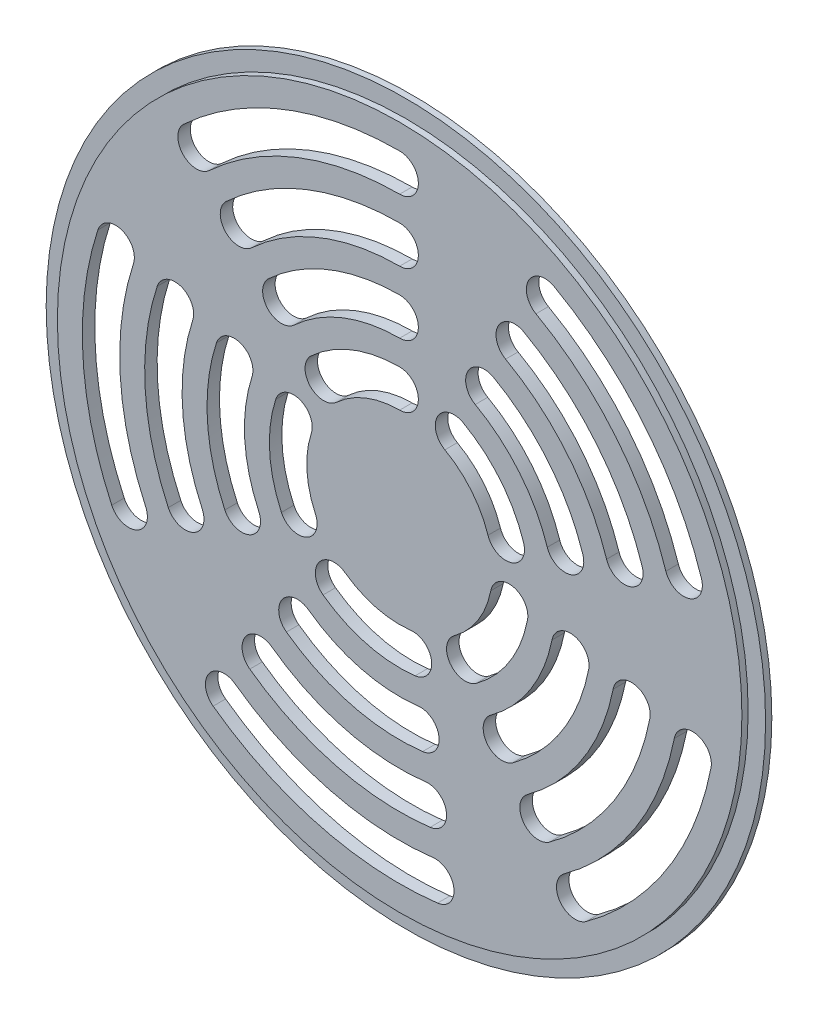
SolidWorks part; units mm, degrees
ref_plane "Plan de face" through (0, 0, 0) normal (0, 0, 1) x (1, 0, 0)
ref_plane "Plan de dessus" through (0, 0, 0) normal (0, 1, 0) x (1, 0, 0)
ref_plane "Plan de droite" through (0, 0, 0) normal (1, 0, 0) x (0, 0, -1)
sketch "Esquisse1" plane through (0, 0, 0) normal (0, 0, 1) x (1, 0, 0)
  line L0 (-32.5805, 35.1129) -> (-25.7788, 27.7825) construction
  line L1 (-25.7788, 27.7825) -> (0, 0) construction
  line L2 (23.3265, 41.8364) -> (18.4566, 33.1023) construction
  line L3 (46.9971, -9.2566) -> (37.1856, -7.3241) construction
  line L4 (5.7193, -47.5573) -> (4.5253, -37.6289) construction
  line L5 (-43.4623, -20.1354) -> (-34.3888, -15.9318) construction
  circle A0 centre (0, 0) radius 54.9
  arc A1 (0, 50.9) -> (-34.6211, 37.3121) centre (0, 0) ccw
  arc A2 (0, 44.9) -> (-30.54, 32.9138) centre (0, 0) ccw
  circle A3 centre (0, 47.9) radius 3
  circle A4 centre (-32.5805, 35.1129) radius 3
  arc A5 (48.4088, 15.729) -> (24.7874, 44.4567) centre (0, 0) ccw
  arc A6 (42.7024, 13.8749) -> (21.8655, 39.2162) centre (0, 0) ccw
  circle A7 centre (45.5556, 14.8019) radius 3
  circle A8 centre (23.3265, 41.8364) radius 3
  arc A9 (29.9183, -41.179) -> (49.9405, -9.8364) centre (0, 0) ccw
  arc A10 (26.3916, -36.3249) -> (44.0536, -8.6769) centre (0, 0) ccw
  circle A11 centre (28.1549, -38.7519) radius 3
  circle A12 centre (46.9971, -9.2566) radius 3
  arc A13 (-29.9183, -41.179) -> (6.0775, -50.5359) centre (0, 0) ccw
  arc A14 (-26.3916, -36.3249) -> (5.3611, -44.5788) centre (0, 0) ccw
  circle A15 centre (-28.1549, -38.7519) radius 3
  circle A16 centre (5.7193, -47.5573) radius 3
  arc A17 (-48.4088, 15.729) -> (-46.1844, -21.3965) centre (0, 0) ccw
  arc A18 (-42.7024, 13.8749) -> (-40.7403, -18.8743) centre (0, 0) ccw
  circle A19 centre (-45.5556, 14.8019) radius 3
  circle A20 centre (-43.4623, -20.1354) radius 3
  arc A21 (0, 40.9) -> (-27.8193, 29.9816) centre (0, 0) ccw
  arc A22 (0, 34.9) -> (-23.7382, 25.5833) centre (0, 0) ccw
  circle A23 centre (0, 37.9) radius 3
  circle A24 centre (-25.7788, 27.7825) radius 3
  arc A25 (38.8982, 12.6388) -> (19.9176, 35.7225) centre (0, 0) ccw
  arc A26 (33.1919, 10.7847) -> (16.9957, 30.4821) centre (0, 0) ccw
  circle A27 centre (36.045, 11.7117) radius 3
  circle A28 centre (18.4566, 33.1023) radius 3
  arc A29 (24.0404, -33.0888) -> (40.129, -7.9039) centre (0, 0) ccw
  arc A30 (20.5137, -28.2347) -> (34.2421, -6.7444) centre (0, 0) ccw
  circle A31 centre (22.2771, -30.6617) radius 3
  circle A32 centre (37.1856, -7.3241) radius 3
  arc A33 (-24.0404, -33.0888) -> (4.8835, -40.6074) centre (0, 0) ccw
  arc A34 (-20.5137, -28.2347) -> (4.1671, -34.6503) centre (0, 0) ccw
  circle A35 centre (-22.2771, -30.6617) radius 3
  circle A36 centre (4.5253, -37.6289) radius 3
  arc A37 (-38.8982, 12.6388) -> (-37.1108, -17.1929) centre (0, 0) ccw
  arc A38 (-33.1919, 10.7847) -> (-31.6667, -14.6707) centre (0, 0) ccw
  circle A39 centre (-36.045, 11.7117) radius 3
  circle A40 centre (-34.3888, -15.9318) radius 3
  arc A41 (0, 30.9) -> (-21.0175, 22.6511) centre (0, 0) ccw
  arc A42 (0, 24.9) -> (-16.9364, 18.2529) centre (0, 0) ccw
  circle A43 centre (0, 27.9) radius 3
  circle A44 centre (-18.977, 20.452) radius 3
  arc A45 (29.3876, 9.5486) -> (15.0478, 26.9884) centre (0, 0) ccw
  arc A46 (23.6813, 7.6945) -> (12.1259, 21.748) centre (0, 0) ccw
  circle A47 centre (26.5345, 8.6216) radius 3
  circle A48 centre (13.5868, 24.3682) radius 3
  arc A49 (18.1626, -24.9986) -> (30.3175, -5.9714) centre (0, 0) ccw
  arc A50 (14.6359, -20.1445) -> (24.4306, -4.8119) centre (0, 0) ccw
  circle A51 centre (16.3992, -22.5716) radius 3
  circle A52 centre (27.3741, -5.3916) radius 3
  arc A53 (-18.1626, -24.9986) -> (3.6895, -30.6789) centre (0, 0) ccw
  arc A54 (-14.6359, -20.1445) -> (2.9731, -24.7219) centre (0, 0) ccw
  circle A55 centre (-16.3992, -22.5716) radius 3
  circle A56 centre (3.3313, -27.7004) radius 3
  arc A57 (-29.3876, 9.5486) -> (-28.0373, -12.9892) centre (0, 0) ccw
  arc A58 (-23.6813, 7.6945) -> (-22.5932, -10.4671) centre (0, 0) ccw
  circle A59 centre (-26.5345, 8.6216) radius 3
  circle A60 centre (-25.3152, -11.7282) radius 3
  arc A61 (0, 20.9) -> (-14.2157, 15.3207) centre (0, 0) ccw
  arc A62 (0, 14.9) -> (-10.1347, 10.9224) centre (0, 0) ccw
  circle A63 centre (0, 17.9) radius 3
  circle A64 centre (-12.1752, 13.1215) radius 3
  arc A65 (19.8771, 6.4585) -> (10.1779, 18.2543) centre (0, 0) ccw
  arc A66 (14.1707, 4.6044) -> (7.256, 13.0138) centre (0, 0) ccw
  circle A67 centre (17.0239, 5.5314) radius 3
  circle A68 centre (8.717, 15.6341) radius 3
  arc A69 (12.2847, -16.9085) -> (20.506, -4.0389) centre (0, 0) ccw
  arc A70 (8.758, -12.0544) -> (14.6191, -2.8794) centre (0, 0) ccw
  circle A71 centre (10.5214, -14.4814) radius 3
  circle A72 centre (17.5626, -3.4592) radius 3
  arc A73 (-12.2847, -16.9085) -> (2.4955, -20.7505) centre (0, 0) ccw
  arc A74 (-8.758, -12.0544) -> (1.7791, -14.7934) centre (0, 0) ccw
  circle A75 centre (-10.5214, -14.4814) radius 3
  circle A76 centre (2.1373, -17.7719) radius 3
  arc A77 (-19.8771, 6.4585) -> (-18.9637, -8.7856) centre (0, 0) ccw
  arc A78 (-14.1707, 4.6044) -> (-13.5196, -6.2634) centre (0, 0) ccw
  circle A79 centre (-17.0239, 5.5314) radius 3
  circle A80 centre (-16.2417, -7.5245) radius 3
  point P46 (0, 0)
  point P92 (0, 0)
  point P134 (0, 0)
  point P144 (0, 0)
  point P145 (0, 0)
  point P147 (0, 0)
  point P155 (0, 0)
  point P156 (0, 0)
  point P158 (0, 0)
  point P166 (0, 0)
  point P167 (0, 0)
  point P169 (0, 0)
  point P177 (0, 0)
  point P178 (0, 0)
  point P180 (0, 0)
  point P188 (0, 0)
  dimension "D1" = 109.8
  dimension "D2" = 6
  dimension "D3" = 4
  dimension "D5" = 5
  dimension "D7" = 4
  dimension "D8" = 6
  dimension "D9" = 4
  dimension "D10" = 6
  dimension "D12" = 4
  dimension "D13" = 6
  dimension "D4" = 35
  dimension "D6" = 5
  dimension "D11" = 5
  dimension "D14" = 5
extrude "Boss.-Extru.1" add sketch "Esquisse1" along normal blind 2 contours A0 A64 A61 A63 A62 A60 A57 A59 A58 A56 A53 A55 A54 A52 A49 A51 A50 A48 A45 A47 A46 A44 A41 A43 A42 A40 A37 A39 A38 A36 A33 A35 A34 A32 A29 A31 A30 A28 A25 A27 A26
sketch "Esquisse3" plane through (0, 0, 0) normal (0, 0, -1) x (-1, 0, 0)
  circle A0 centre (0, 0) radius 57.7
  circle A1 centre (0, 0) radius 54.9
  circle A2 centre (0, 0) radius 54.9 construction
  dimension "D1" = 2.8
extrude "Boss.-Extru.2" add sketch "Esquisse3" against normal blind 1 separate body
